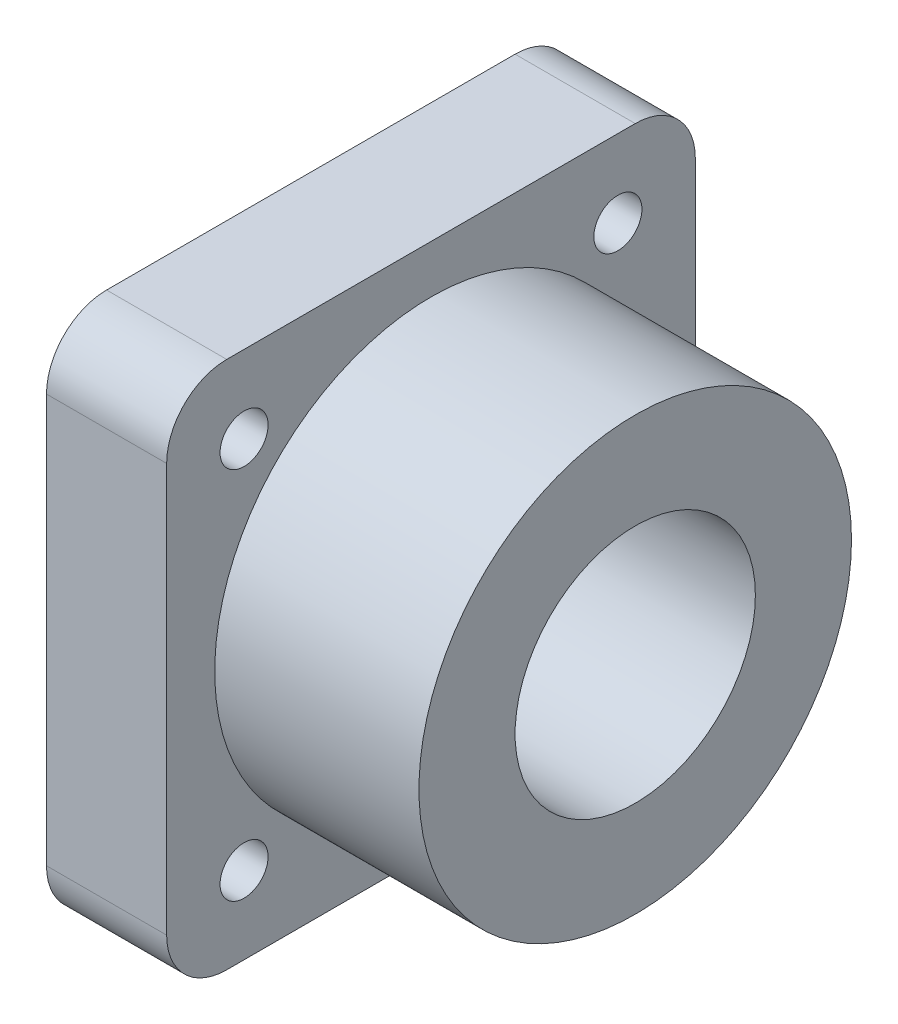
SolidWorks part; units mm, degrees
ref_plane "Front Plane" through (0, 0, 0) normal (0, 0, 1) x (1, 0, 0)
ref_plane "Top Plane" through (0, 0, 0) normal (0, 1, 0) x (1, 0, 0)
ref_plane "Right Plane" through (0, 0, 0) normal (1, 0, 0) x (0, 0, -1)
sketch "Sketch1" plane through (0, 0, 0) normal (1, 0, 0) x (0, 0, -1)
  line L1 (22, -22) -> (-22, -22)
  line L2 (22, -22) -> (22, 22)
  line L3 (22, 22) -> (-22, 22)
  line L4 (-22, -22) -> (-22, 22)
  line L5 (22, -22) -> (-22, 22) construction
  line L6 (22, 22) -> (-22, -22) construction
  circle A0 centre (-15.5563, 15.5563) radius 2
  circle A1 centre (15.5563, 15.5563) radius 2
  circle A2 centre (15.5563, -15.5563) radius 2
  circle A3 centre (-15.5563, -15.5563) radius 2
  circle A4 centre (0, 0) radius 10
  point P0 (0, 0)
  dimension "D2" = 4
  dimension "D4" = 20
  dimension "D1" = 44
  dimension "D3" = 44
extrude "Boss-Extrude1" add sketch "Sketch1" along normal blind 10
sketch "Sketch2" plane through (0, 0, 0) normal (1, 0, 0) x (0, 0, -1)
  circle A0 centre (0, 0) radius 18
  circle A1 centre (0, 0) radius 10
  dimension "D1" = 20
  dimension "D2" = 36
extrude "Boss-Extrude2" add sketch "Sketch2" along normal blind 27
fillet "Fillet1" radius 5 4 edges at (5, 22, 22) (5, 22, -22) (5, -22, -22) (5, -22, 22)
